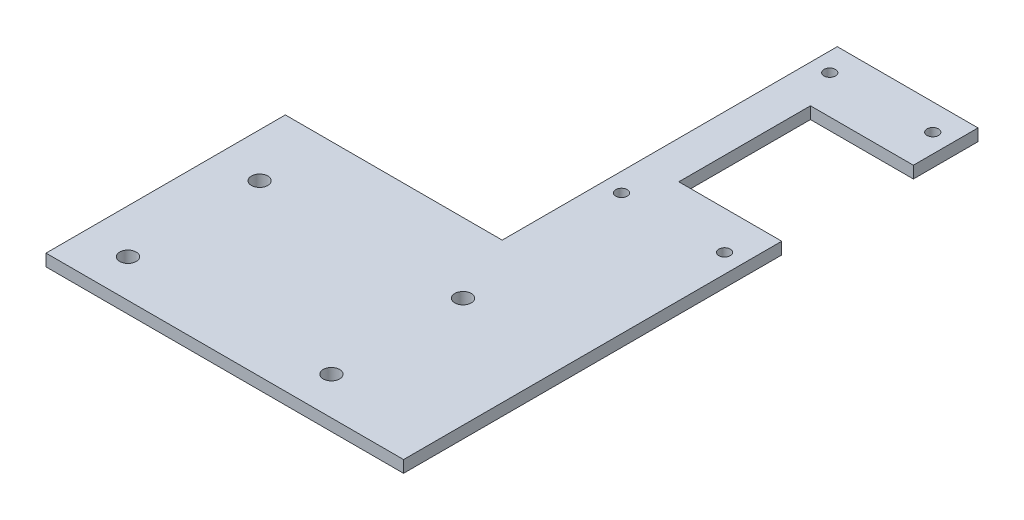
SolidWorks part; units mm, degrees
material "ASTM A36 Steel"
ref_plane "Front Plane" through (0, 0, 0) normal (0, 0, 1) x (1, 0, 0)
ref_plane "Top Plane" through (0, 0, 0) normal (0, 1, 0) x (1, 0, 0)
ref_plane "Right Plane" through (0, 0, 0) normal (1, 0, 0) x (0, 0, -1)
sketch "Sketch1" plane through (0, 0, 0) normal (0, 1, 0) x (1, 0, 0)
  line L0 (77.7316, 152.4) -> (77.7316, -25.4)
  line L1 (-152.4, -152.4) -> (152.4, -152.4)
  line L2 (-152.4, -152.4) -> (-152.4, 152.4)
  line L3 (-152.4, 152.4) -> (152.4, 152.4)
  line L4 (152.4, -152.4) -> (152.4, 152.4)
  line L5 (-152.4, -152.4) -> (152.4, 152.4) construction
  line L6 (-152.4, 152.4) -> (152.4, -152.4) construction
  line L7 (77.7316, -25.4) -> (-152.4, -25.4)
  line L8 (152.4, 118.11) -> (97.79, 118.11)
  line L9 (97.79, 118.11) -> (97.79, 48.26)
  line L10 (97.79, 48.26) -> (152.4, 48.26)
  line L11 (40.0634, -5.1137) -> (40.0634, -72.0577) construction
  line L12 (-37.3342, -25.4) -> (-37.3342, -152.4)
  circle A0 centre (142.367, 138.43) radius 3.048
  circle A1 centre (87.6884, 138.43) radius 3.048
  circle A2 centre (142.367, 27.94) radius 3.048
  circle A3 centre (87.6884, 27.94) radius 3.048
  circle A4 centre (-13.9116, -62.484) radius 4.3688
  circle A5 centre (94.0384, -62.484) radius 4.3688
  circle A6 centre (-13.9116, -132.334) radius 4.3688
  circle A7 centre (94.0384, -132.334) radius 4.3688
  point P0 (0, 0)
  dimension "D3" = 74.6684
  dimension "D4" = 6.096
  dimension "D8" = 177.8
  dimension "D9" = 34.29
  dimension "D13" = 8.7376
  dimension "D1" = 304.8
  dimension "D2" = 304.8
  dimension "D5" = 110.49
  dimension "D6" = 10.033
  dimension "D7" = 54.6786
  dimension "D10" = 69.85
  dimension "D11" = 20.0584
  dimension "D12" = 13.97
  dimension "D14" = 69.85
  dimension "D15" = 107.95
  dimension "D16" = 90.424
  dimension "D17" = 101.6
extrude "Boss-Extrude1" add sketch "Sketch1" along normal blind 6.35 contours L0 L7 L2 L1 L4 L3 A3 A2 A1 A0
